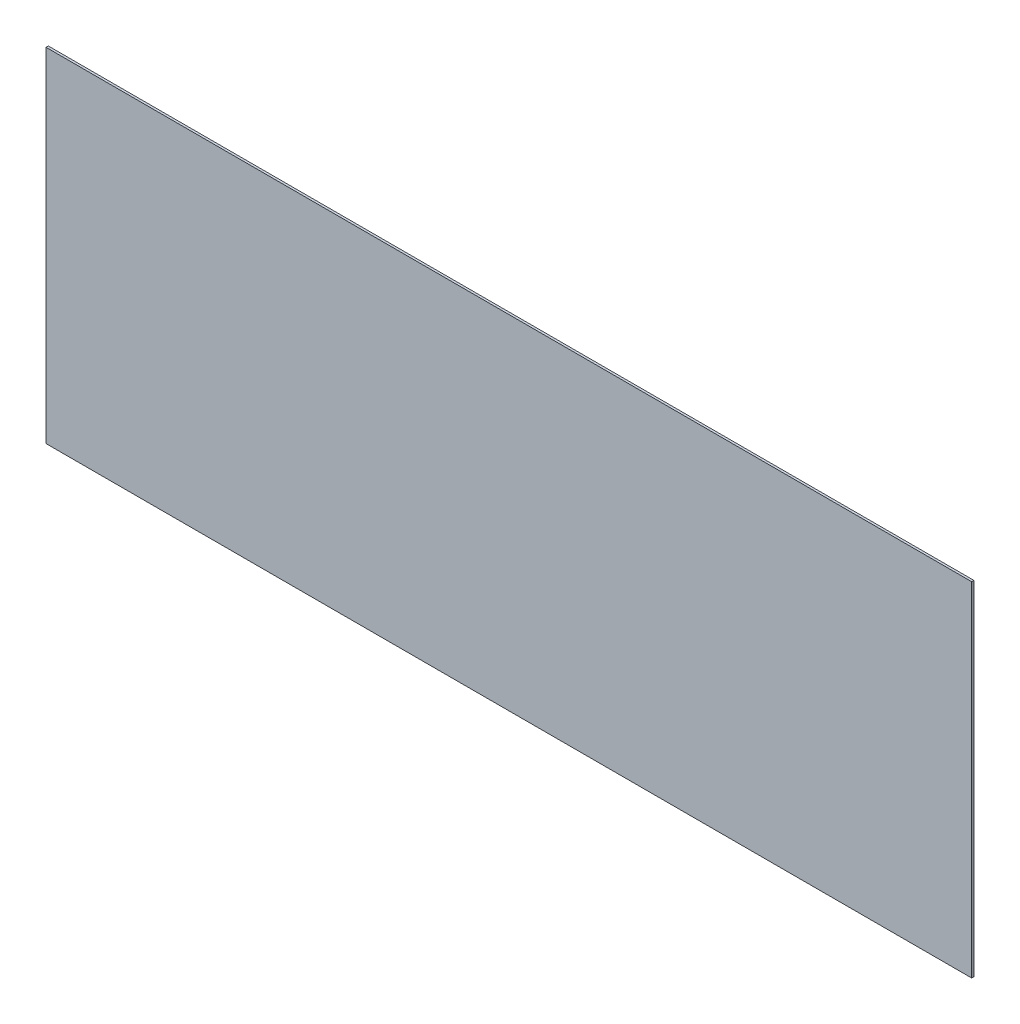
SolidWorks part; units mm, degrees
material "Acrylic (Medium-high impact)"
ref_plane "Front Plane" through (0, 0, 0) normal (0, 0, 1) x (1, 0, 0)
ref_plane "Top Plane" through (0, 0, 0) normal (0, 1, 0) x (1, 0, 0)
ref_plane "Right Plane" through (0, 0, 0) normal (1, 0, 0) x (0, 0, -1)
sketch "Sketch1" plane through (0, 0, 0) normal (0, 0, 1) x (1, 0, 0)
  line L1 (-609.6, 226.06) -> (609.6, 226.06)
  line L2 (-609.6, 226.06) -> (-609.6, -226.06)
  line L3 (-609.6, -226.06) -> (609.6, -226.06)
  line L4 (609.6, 226.06) -> (609.6, -226.06)
  line L5 (-609.6, 226.06) -> (609.6, -226.06) construction
  line L6 (-609.6, -226.06) -> (609.6, 226.06) construction
  point P0 (0, 0)
  dimension "D1" = 1219.2
  dimension "D2" = 452.12
extrude "Boss-Extrude1" add sketch "Sketch1" along normal blind 2.9972
